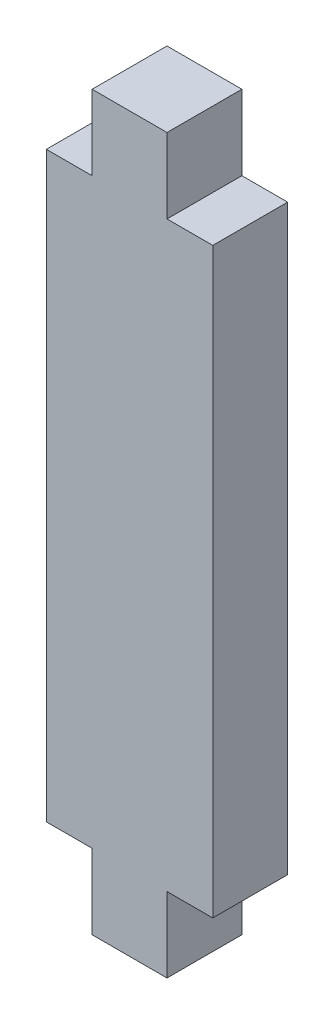
SolidWorks part; units mm, degrees
ref_plane "Front Plane" through (0, 0, 0) normal (0, 0, 1) x (1, 0, 0)
ref_plane "Top Plane" through (0, 0, 0) normal (0, 1, 0) x (1, 0, 0)
ref_plane "Right Plane" through (0, 0, 0) normal (1, 0, 0) x (0, 0, -1)
sketch "Sketch2" plane through (0, 0, 0) normal (0, 0, 1) x (1, 0, 0)
  line L1 (-5, 17.5) -> (5, 17.5)
  line L2 (-5, 17.5) -> (-5, 0)
  line L3 (-5, 0) -> (5, 0)
  line L4 (5, 17.5) -> (5, 0)
  line L5 (-2.25, 22) -> (2.25, 22)
  line L6 (-2.25, 22) -> (-2.25, 17.5)
  line L7 (-2.25, 17.5) -> (2.25, 17.5)
  line L8 (2.25, 22) -> (2.25, 17.5)
  dimension "D1" = 10
  dimension "D2" = 17.5
  dimension "D3" = 4.5
  dimension "D4" = 4.5
  dimension "D5" = 5
  dimension "D6" = 17.5
  dimension "D7" = 2.25
extrude "Boss-Extrude1" add sketch "Sketch2" against normal mid plane 4.5 contours L8 L5 L6 L1 | L4 L1 L2 L3
mirror "Mirror1" about plane through (0, 0, 0) normal (0, 1, 0) of bodies 101
equation "\"D5@Sketch2\"=(\"D1@Sketch2\")/2"
equation "\"D6@Sketch2\"=(\"D2@Sketch2\")"
equation "\"D7@Sketch2\"=(\"D3@Sketch2\")/2"
